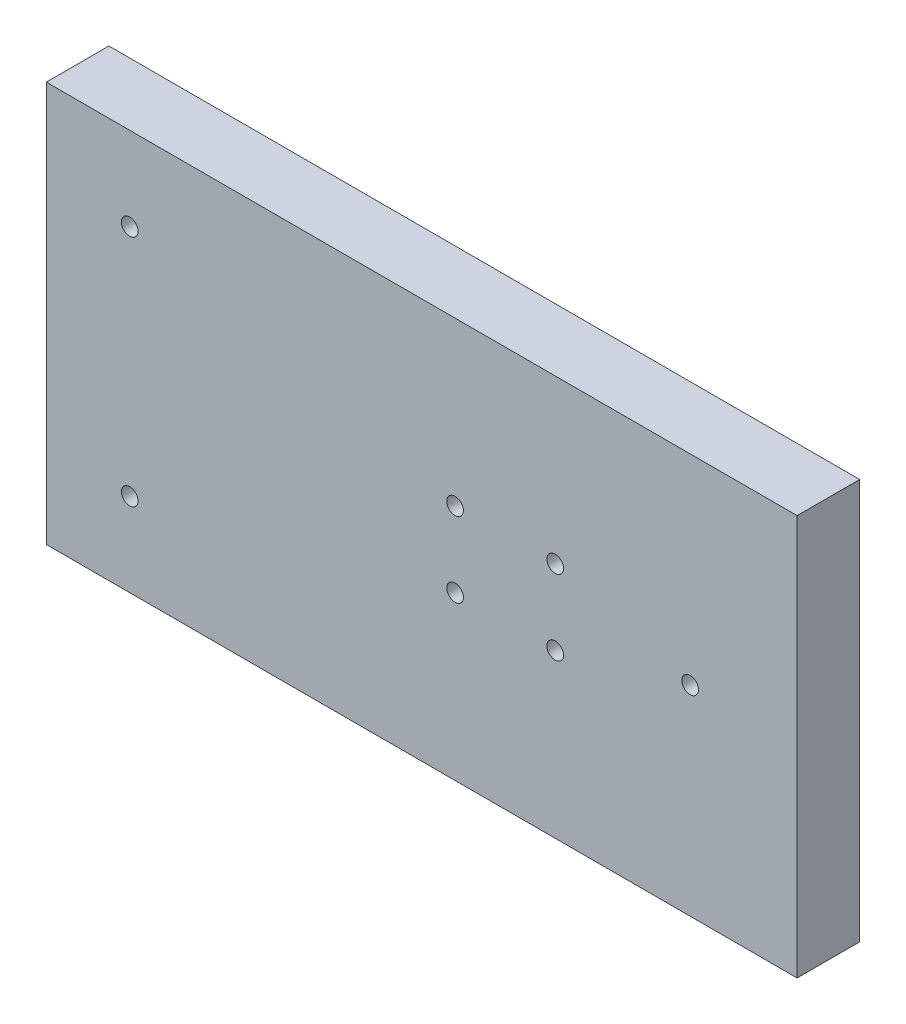
SolidWorks part; units mm, degrees
material "Balsa"
ref_plane "Front Plane" through (0, 0, 0) normal (0, 0, 1) x (1, 0, 0)
ref_plane "Top Plane" through (0, 0, 0) normal (0, 1, 0) x (1, 0, 0)
ref_plane "Right Plane" through (0, 0, 0) normal (1, 0, 0) x (0, 0, -1)
sketch "Sketch1" plane through (0, 0, 0) normal (0, 0, 1) x (1, 0, 0)
  line L0 (-705.5345, 268.5094) -> (-525.5345, 268.5094) construction
  line L1 (-705.5345, 220.5094) -> (-525.5345, 220.5094)
  line L2 (-705.5345, 220.5094) -> (-705.5345, 316.5094)
  line L3 (-705.5345, 316.5094) -> (-525.5345, 316.5094)
  line L4 (-525.5345, 220.5094) -> (-525.5345, 316.5094)
  line L21 (-607.5345, 259.5094) -> (-607.5345, 277.5094) construction
  line L22 (-543.1836, 454.05) -> (-543.1836, 104.05) construction
  line L23 (-607.5345, 259.5094) -> (-583.5345, 259.5094) construction
  circle A0 centre (-583.5345, 277.5094) radius 2
  circle A1 centre (-607.5345, 277.5094) radius 2
  circle A2 centre (-583.5345, 259.5094) radius 2
  circle A3 centre (-607.5345, 259.5094) radius 2
  circle A4 centre (-685.5345, 296.5094) radius 2
  circle A5 centre (-685.5345, 240.5094) radius 2
  circle A6 centre (-551.1836, 268.5094) radius 2
  point P24 (-607.5345, 268.5094)
  dimension "D13" = 20
  dimension "D14" = 20
  dimension "D16" = 4
  dimension "D10" = 4
  dimension "D11" = 4
  dimension "D12" = 4
  dimension "D1" = 180
  dimension "D2" = 96
  dimension "D3" = 8
  dimension "D15" = 20
  dimension "D18" = 24
  dimension "D19" = 18
extrude "Boss-Extrude1" add sketch "Sketch1" along normal blind 15
